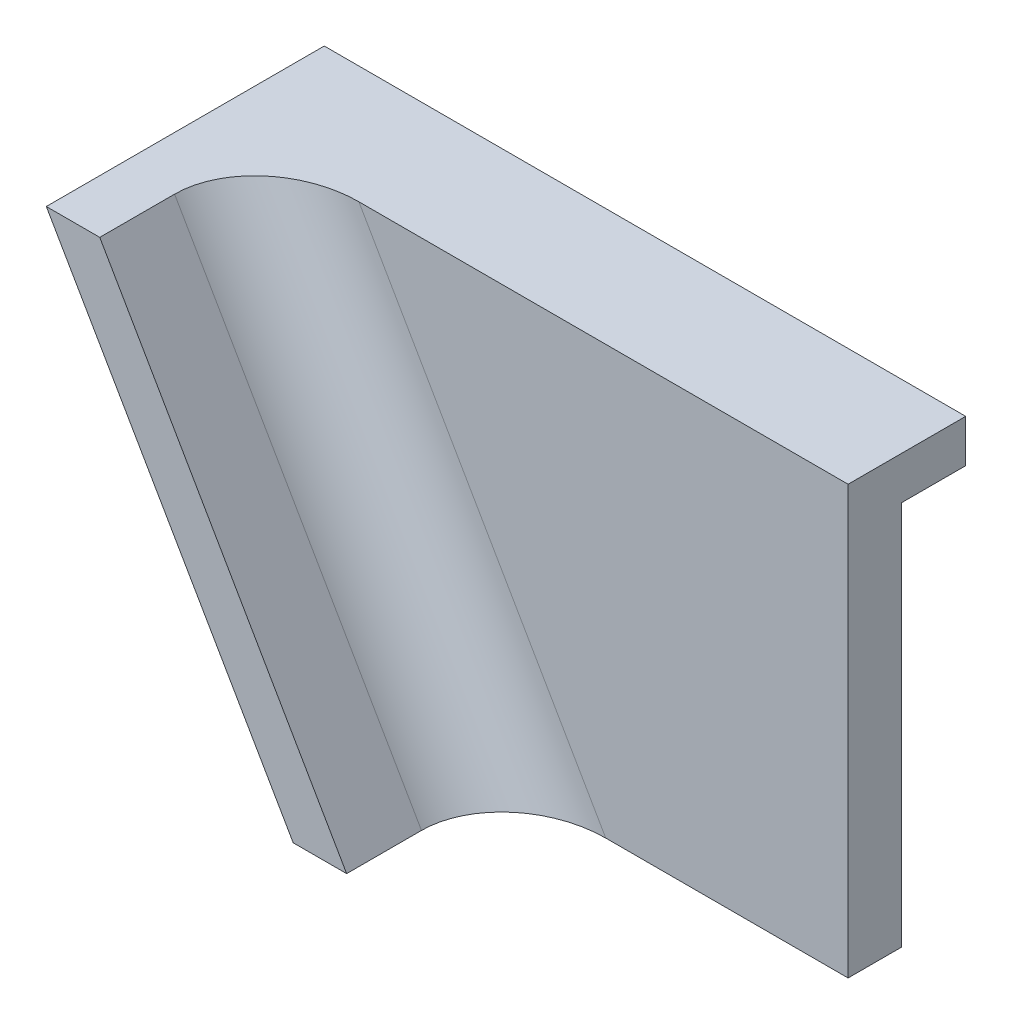
SolidWorks part; units mm, degrees
ref_plane "Front Plane" through (0, 0, 0) normal (0, 0, 1) x (1, 0, 0)
ref_plane "Top Plane" through (0, 0, 0) normal (0, 1, 0) x (1, 0, 0)
ref_plane "Right Plane" through (0, 0, 0) normal (1, 0, 0) x (0, 0, -1)
sketch "Sketch1" plane through (0, 0, 0) normal (0, 0, 1) x (1, 0, 0)
  line L0 (0, 0) -> (76.2, 0)
  line L1 (76.2, 0) -> (76.2, -50.8)
  line L2 (0, 0) -> (29.3294, -50.8)
  line L3 (76.2, -50.8) -> (29.3294, -50.8)
  dimension "D1" = 60
  dimension "D2" = 76.2
  dimension "D3" = 50.8
extrude "Boss-Extrude1" add sketch "Sketch1" along normal blind 6.35
sketch "Sketch2" plane through (0, 0, 0) normal (0, 0, 1) x (1, 0, 0)
  line L0 (76.2, 0) -> (0, 0)
  line L1 (76.2, 0) -> (76.2, -5.08)
  line L2 (76.2, -50.8) -> (76.2, 0) construction
  line L3 (76.2, -5.08) -> (2.9329, -5.08)
  line L4 (0, 0) -> (2.9329, -5.08)
  dimension "D1" = 5.08
extrude "Boss-Extrude2" add sketch "Sketch2" against normal blind 7.62
ref_plane "Plane1" through (0, 0, 6.35) normal (0, 0, 1) x (1, 0, 0)
sketch "Sketch3" plane through (0, 0, 6.35) normal (0, 0, 1) x (1, 0, 0)
  line L0 (0, 0) -> (6.35, 0)
  line L1 (76.2, 0) -> (0, 0) construction
  line L2 (0, 0) -> (29.3294, -50.8)
  line L3 (29.3294, -50.8) -> (35.6794, -50.8)
  line L4 (29.3294, -50.8) -> (76.2, -50.8) construction
  line L5 (35.6794, -50.8) -> (6.35, 0)
  line L6 (6.35, 0) -> (6.3875, -0.0472)
  dimension "D1" = 6.35
  dimension "D2" = 6.35
extrude "Boss-Extrude3" add sketch "Sketch3" along normal blind 19.05 contours L3 L5 L0 L2
fillet "Fillet1" radius 10.16 1 edges
